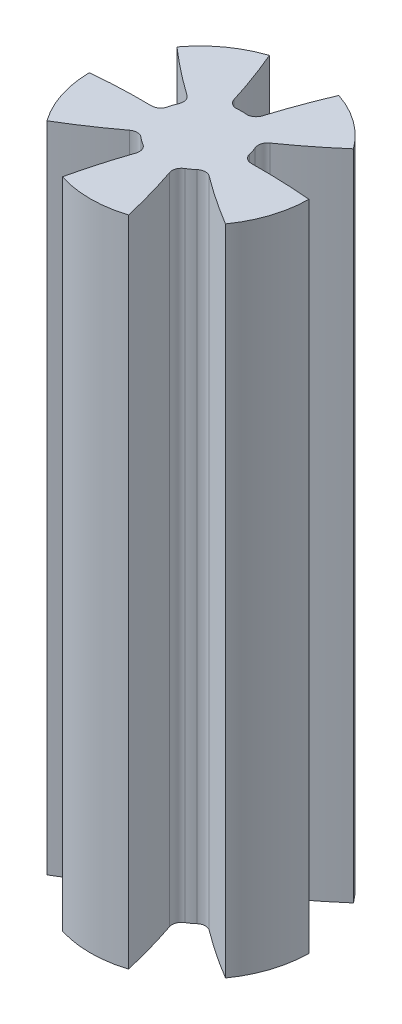
SolidWorks part; units mm, degrees
ref_plane "Front Plane" through (0, 0, 0) normal (0, 0, 1) x (1, 0, 0)
ref_plane "Top Plane" through (0, 0, 0) normal (0, 1, 0) x (1, 0, 0)
ref_plane "Right Plane" through (0, 0, 0) normal (1, 0, 0) x (0, 0, -1)
sketch "Sketch1" plane through (0, 0, 0) normal (0, 1, 0) x (1, 0, 0)
  circle A0 centre (0, 0) radius 3.6 construction
  circle A1 centre (0, 0) radius 5.04
  circle A4 centre (0, 0) radius 1.92
  dimension "D1" = 7.2
  dimension "D2" = 10.08
  dimension "D3" = 3.12
extrude "Boss-Extrude1" add sketch "Sketch1" along normal mid plane 30 contours A1
sketch "Sketch2" plane through (0, 0, 0) normal (0, 1, 0) x (1, 0, 0)
  line L0 (0, 0) -> (0, 5.04) construction
  line L1 (-1.0636, 3.4393) -> (1.0636, 3.4393) construction
  line L2 (0, 0) -> (-0.5398, 1.8426) construction
  line L3 (0, 0.517) -> (-1.5566, 4.7936) construction
  line L4 (0, 0) -> (2.9624, 4.0774) construction
  line L5 (1.0636, 3.4393) -> (2.9423, 2.0744) construction
  circle A0 centre (0, 0) radius 5.04 construction
  arc A1 (-1.5943, 4.7812) -> (-0.5398, 1.8426) centre (-25.7035, -5.5289) cw
  arc A2 (1.5943, 4.7812) -> (0.5398, 1.8426) centre (25.7035, -5.5289) ccw
  circle A3 centre (0, 0) radius 1.92 construction
  arc A4 (1.5943, 4.7812) -> (-1.5943, 4.7812) centre (0, 0) ccw
  arc A5 (0.5398, 1.8426) -> (-0.5398, 1.8426) centre (0, 0) ccw
  circle A6 centre (0, 0) radius 5.04 construction
  circle A7 centre (0, 0) radius 3.6 construction
  point P18 (5.5945, 1.371)
  point P19 (2.1066, 7.8161)
  point P22 (2.243, 7.961)
  point P23 (2.243, 7.961)
  point P24 (2.311, 7.8676)
  point P25 (2.311, 7.8676)
  point P26 (2.1916, 7.9017)
  point P30 (2.3944, 7.8426)
  point P31 (8.8771, 7.747)
  point P32 (0.552, 4.1636)
  point P33 (1.7102, 6.9939)
  dimension "D5" = 1.92
  dimension "D6" = 1.92
  dimension "D1" = 20
  dimension "D2" = 36
  dimension "D4" = 2.3222
extrude "Cut-Extrude1" cut sketch "Sketch2" against normal mid plane 30
ref_plane "Plane1" through (0.5398, 15, -1.8426) normal (0, 1, 0) x (1, 0, 0)
fillet "Fillet2" radius 0.43 2 edges at (0.5398, 0, -1.8426) (-0.5398, 0, -1.8426)
pattern_circular "CirPattern1" count 5 over 360 about axis through (0, 0, 0) along (0, 1, 0) of "Cut-Extrude1", "Fillet2"
equation "\"Module\"= 1.44"
equation "\"Number of teeth\" = 5"
equation "\"Pressure Angle\"= 20"
equation "\"Pitch Diameter\" = \"Pressure Angle\" * \"Module\""
equation "\"Outer Diameter\" = ( \"Number of teeth\" + 2 ) * \"Module\""
equation "\"Tooth Thickness\"= 2.27"
equation "\"Whole Depth\"= 3.12"
equation "\"Working Depth\" = ( 2 * \"Pitch Diameter\" ) / ( \"Number of teeth\" )"
equation "\"Clearance\"= 0.23"
equation "\"D1@Sketch1\"=\"Module\"*\"Number of teeth\""
equation "\"D1@Boss-Extrude1\"=30mm"
equation "\"D1@Sketch2\"=\"Pressure Angle\""
equation "\"D2@Sketch2\"=180/\"Number of teeth\""
equation "\"DC1@Fillet\"=\"Module\"*.3"
equation "\"D2@Sketch1\"=\"Module\"*(\"Number of teeth\"+2)"
equation "\"D3@Sketch1\"=\"Whole Depth\""
equation "\"D1@CirPattern1\"=\"Number of teeth\""
